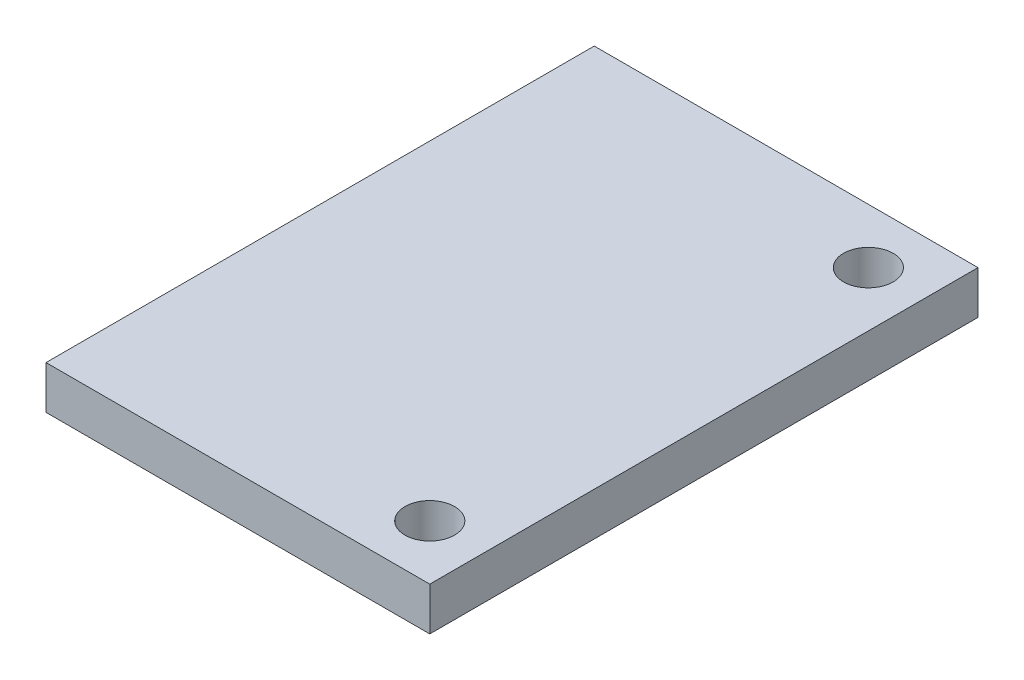
SolidWorks part; units mm, degrees
ref_plane "Front Plane" through (0, 0, 0) normal (0, 0, 1) x (1, 0, 0)
ref_plane "Top Plane" through (0, 0, 0) normal (0, 1, 0) x (1, 0, 0)
ref_plane "Right Plane" through (0, 0, 0) normal (1, 0, 0) x (0, 0, -1)
sketch "Sketch2" plane through (0, 0, 0) normal (0, 1, 0) x (1, 0, 0)
  line L1 (-8.89, 12.7) -> (8.89, 12.7)
  line L2 (-8.89, 12.7) -> (-8.89, -12.7)
  line L3 (-8.89, -12.7) -> (8.89, -12.7)
  line L4 (8.89, 12.7) -> (8.89, -12.7)
  line L5 (-8.89, 12.7) -> (8.89, -12.7) construction
  line L6 (-8.89, -12.7) -> (8.89, 12.7) construction
  point P0 (0, 0)
  dimension "D1" = 17.78
  dimension "D2" = 25.4
extrude "Boss-Extrude1" add sketch "Sketch2" along normal blind 2
sketch "Sketch3" plane through (0, 2, 0) normal (0, 1, 0) x (1, 0, 0)
  line L0 (-8.89, 12.7) -> (-8.89, -12.7) construction
  line L1 (-8.89, 10.16) -> (6.35, 10.16) construction
  line L2 (-8.89, 10.16) -> (-8.89, -10.16) construction
  line L3 (-8.89, -10.16) -> (6.35, -10.16) construction
  line L4 (6.35, 10.16) -> (6.35, -10.16) construction
  line L6 (-8.89, 0) -> (8.89, 0) construction
  line L7 (8.89, -12.7) -> (8.89, 12.7) construction
  circle A0 centre (6.35, 10.16) radius 1.15
  circle A1 centre (6.35, -10.16) radius 1.15
  dimension "D1" = 2.3
  dimension "D2" = 15.24
  dimension "D3" = 20.32
extrude "Cut-Extrude1" cut sketch "Sketch3" against normal up to surface (2 mm away) up to face at (0, 0, 0)
